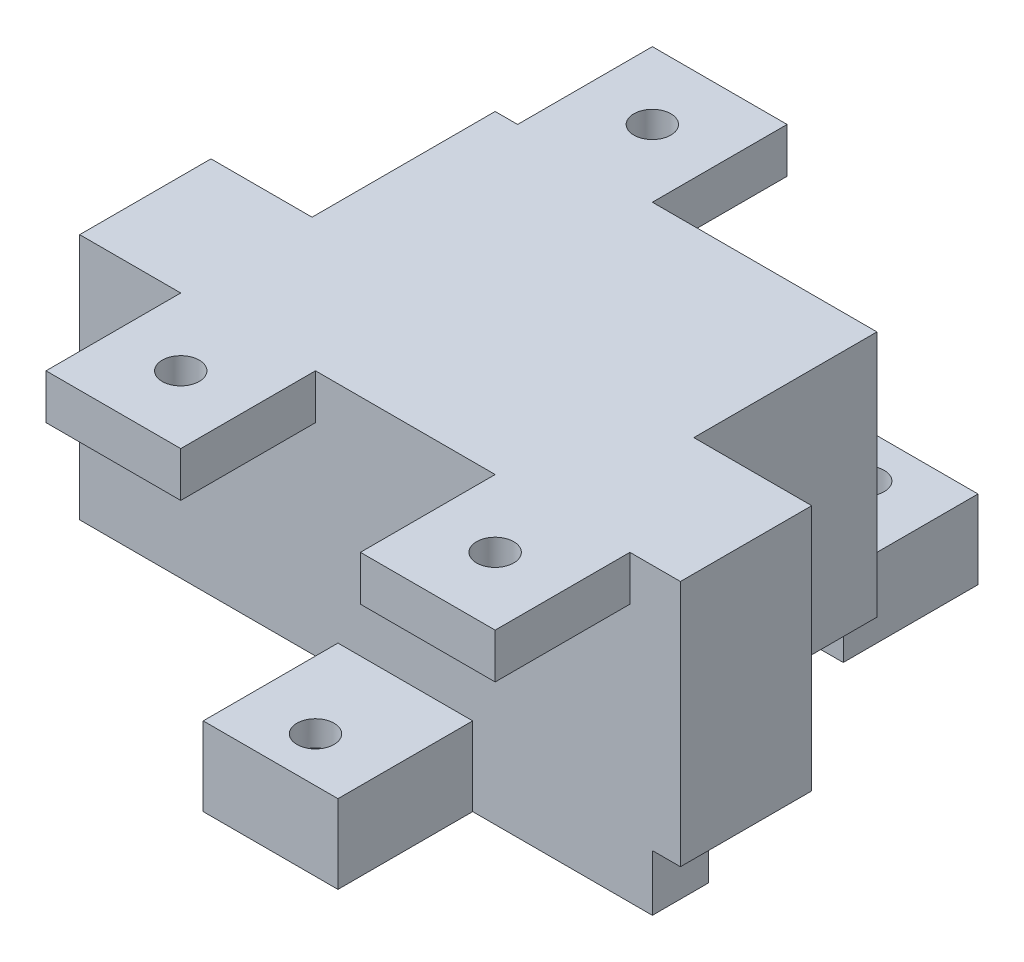
SolidWorks part; units mm, degrees
ref_plane "Front Plane" through (0, 0, 0) normal (0, 0, 1) x (1, 0, 0)
ref_plane "Top Plane" through (0, 0, 0) normal (0, 1, 0) x (1, 0, 0)
ref_plane "Right Plane" through (0, 0, 0) normal (1, 0, 0) x (0, 0, -1)
sketch "Sketch1" plane through (0, 0, 0) normal (0, 1, 0) x (1, 0, 0)
  line L0 (0, 0) -> (28, 0)
  line L1 (28, 0) -> (28, 5)
  line L2 (28, 5) -> (7, 5)
  line L3 (7, 5) -> (7, 23)
  line L4 (7, 23) -> (15, 23)
  line L5 (15, 23) -> (15, 28)
  line L6 (15, 28) -> (0, 28)
  line L7 (0, 28) -> (0, 0)
  dimension "D1" = 7
  dimension "D2" = 28
  dimension "D3" = 15
  dimension "D4" = 5
  dimension "D5" = 5
  dimension "D6" = 28
extrude "Boss-Extrude1" add sketch "Sketch1" along normal blind 5
sketch "Sketch2" plane through (0, 5, 0) normal (0, 1, 0) x (1, 0, 0)
  line L1 (-14, 0) -> (20, 0)
  line L2 (-14, 0) -> (-14, 28)
  line L3 (-14, 28) -> (20, 28)
  line L4 (20, 0) -> (20, 28)
  line L5 (0, 28) -> (0, 0) construction
  line L6 (-23, 0) -> (30.5, 0)
  line L7 (-23, 0) -> (-23, 11.6938)
  line L8 (-23, 11.6938) -> (30.5, 11.6938)
  line L9 (30.5, 0) -> (30.5, 11.6938)
  line M7 (0, 28) -> (0, 0)
  line M8 (0, 0) -> (28, 0)
  line M9 (28, 0) -> (28, 5)
  line M10 (28, 5) -> (7, 5)
  line M11 (7, 5) -> (7, 23)
  line M12 (7, 23) -> (15, 23)
  line M13 (15, 23) -> (15, 28)
  line M14 (15, 28) -> (0, 28)
  dimension "D1" = 34
  dimension "D2" = 28
  dimension "D3" = 14
  dimension "D4" = 53.5
  dimension "D5" = 23
extrude "Boss-Extrude2" add sketch "Sketch2" along normal blind 22 contours L8 L2 L1 M7 | L8 L7 L6 L2 | L2 L8 L3 M7 | L8 L4 L3 M11 M13 M12 | L8 L4 M11 M10 | L6 L9 L8 L4 M10 M9 | L8 L4 M7 M8 M10 M11 | L8 M7 M11 M12 M13 M14 | L4 M8 M9 M10
sketch "Sketch3" plane through (0, 27, 0) normal (0, 1, 0) x (1, 0, 0)
  line L0 (-14, 28) -> (20, 28) construction
  line L1 (5, 28) -> (17, 28)
  line L2 (5, 28) -> (5, 40)
  line L3 (5, 40) -> (17, 40)
  line L4 (17, 28) -> (17, 40)
  line L5 (20, 11.6938) -> (20, 28) construction
  point P6 (0, 0)
  dimension "D1" = 12
  dimension "D2" = 12
  dimension "D3" = 3
extrude "Boss-Extrude3" add sketch "Sketch3" against normal blind 7 from offset 20 offset against normal yes
sketch "Sketch4" plane through (0, 0, 0) normal (0, -1, 0) x (1, 0, 0)
  line L0 (17, -28) -> (17, -40) construction
  line L1 (14.2332, -36) -> (12.6166, -33.2)
  line L2 (12.6166, -33.2) -> (9.3834, -33.2)
  line L3 (9.3834, -33.2) -> (7.7668, -36)
  line L4 (7.7668, -36) -> (9.3834, -38.8)
  line L5 (9.3834, -38.8) -> (12.6166, -38.8)
  line L6 (12.6166, -38.8) -> (14.2332, -36)
  line L7 (17, -40) -> (5, -40) construction
  circle A0 centre (11, -36) radius 2.8 construction
  dimension "D1" = 5.6
  dimension "D2" = 6
  dimension "D3" = 4
extrude "Cut-Extrude1" cut sketch "Sketch4" against normal blind 2.5 from offset 2.25 offset against normal yes
sketch "Sketch5" plane through (0, 0, 0) normal (0, -1, 0) x (1, 0, 0)
  line L0 (17, -28) -> (17, -40) construction
  line L1 (17, -40) -> (5, -40) construction
  circle A0 centre (11, -36) radius 1.65
  dimension "D1" = 3.3
  dimension "D2" = 6
  dimension "D3" = 4
extrude "Cut-Extrude3" cut sketch "Sketch5" against normal through all
sketch "Sketch6" plane through (0, 27, 0) normal (0, 1, 0) x (1, 0, 0)
  line L0 (-14, 28) -> (20, 28) construction
  line L1 (-12, 28) -> (0, 28)
  line L2 (-12, 28) -> (-12, 40)
  line L3 (-12, 40) -> (0, 40)
  line L4 (0, 28) -> (0, 40)
  line L5 (-14, 11.6938) -> (-14, 28) construction
  circle A0 centre (-6, 34) radius 1.65
  dimension "D4" = 3.3
  dimension "D6" = 6
  dimension "D1" = 12
  dimension "D2" = 12
  dimension "D3" = 2
  dimension "D5" = 6
extrude "Boss-Extrude4" add sketch "Sketch6" against normal blind 4
sketch "Sketch7" plane through (0, 27, 0) normal (0, 1, 0) x (1, 0, 0)
  line L0 (-23, 0) -> (30.5, 0) construction
  line L1 (0, 0) -> (12, 0)
  line L2 (0, 0) -> (0, -12)
  line L3 (0, -12) -> (12, -12)
  line L4 (12, 0) -> (12, -12)
  circle A0 centre (6, -8) radius 1.65
  point P10 (0, 0)
  dimension "D3" = 3.3
  dimension "D4" = 4
  dimension "D5" = 6
  dimension "D1" = 12
  dimension "D2" = 12
extrude "Boss-Extrude6" add sketch "Sketch7" against normal blind 7 from offset 20 offset against normal yes
sketch "Sketch8" plane through (0, 0, 0) normal (0, -1, 0) x (1, 0, 0)
  line L1 (9.2332, 8) -> (7.6166, 10.8)
  line L2 (7.6166, 10.8) -> (4.3834, 10.8)
  line L3 (4.3834, 10.8) -> (2.7668, 8)
  line L4 (2.7668, 8) -> (4.3834, 5.2)
  line L5 (4.3834, 5.2) -> (7.6166, 5.2)
  line L6 (7.6166, 5.2) -> (9.2332, 8)
  circle A0 centre (6, 8) radius 2.8 construction
  dimension "D1" = 5.6
extrude "Cut-Extrude4" cut sketch "Sketch8" against normal blind 2.5 from offset 2.25 offset against normal yes
sketch "Sketch9" plane through (0, 27, 0) normal (0, 1, 0) x (1, 0, 0)
  line L0 (-23, 0) -> (30.5, 0) construction
  line L1 (-14, 0) -> (-2, 0)
  line L2 (-14, 0) -> (-14, -12)
  line L3 (-14, -12) -> (-2, -12)
  line L4 (-2, 0) -> (-2, -12)
  line L5 (-23, 0) -> (30.5, 0) construction
  line L6 (14, 0) -> (26, 0)
  line L7 (14, 0) -> (14, -12)
  line L8 (14, -12) -> (26, -12)
  line L9 (26, 0) -> (26, -12)
  line L10 (12, -12) -> (12, 0) construction
  circle A0 centre (-8, -6) radius 1.65
  circle A1 centre (20, -6) radius 1.65
  dimension "D7" = 3.3
  dimension "D8" = 6
  dimension "D9" = 6
  dimension "D10" = 6
  dimension "D11" = 6
  dimension "D1" = 12
  dimension "D2" = 12
  dimension "D3" = 12
  dimension "D4" = 12
  dimension "D5" = 2
  dimension "D6" = 2
extrude "Boss-Extrude7" add sketch "Sketch9" against normal blind 4
